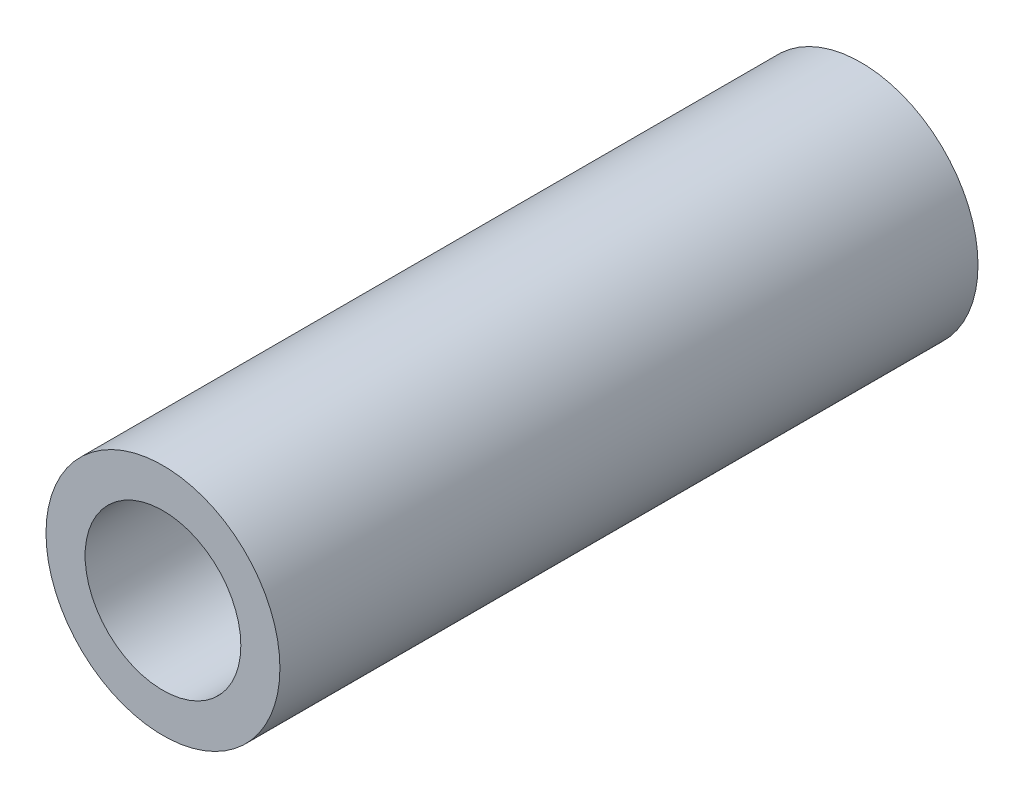
SolidWorks part; units mm, degrees
ref_plane "Front Plane" through (0, 0, 0) normal (0, 0, 1) x (1, 0, 0)
ref_plane "Top Plane" through (0, 0, 0) normal (0, 1, 0) x (1, 0, 0)
ref_plane "Right Plane" through (0, 0, 0) normal (1, 0, 0) x (0, 0, -1)
sketch "Sketch1" plane through (0, 0, 0) normal (0, 0, 1) x (1, 0, 0)
  circle A0 centre (0, 0) radius 4.7879
  circle A1 centre (0, 0) radius 3.1877
  dimension "OD" = 9.5758
  dimension "ID" = 6.3754
sketch "Sketch2" plane through (0, 0, 0) normal (1, 0, 0) x (0, 0, -1)
  line L2 (14.2875, 0) -> (-14.2875, 0) construction
  line L4 (-14.2875, -4.7879) -> (-14.2875, 4.7879) construction
  line L5 (-14.2875, -3.1877) -> (14.2875, -3.1877)
  line L6 (14.2875, 3.1877) -> (-14.2875, 3.1877)
  line L7 (14.2875, -4.7879) -> (14.2875, 4.7879) construction
  line L8 (-14.2875, 4.7879) -> (14.2875, 4.7879) construction
  line L9 (-14.2875, -4.7879) -> (14.2875, -4.7879) construction
  line L10 (0, 4.7879) -> (0, -4.7879) construction
  line L11 (0, 3.1877) -> (0, -3.1877) construction
  point P4 (0, -3.1877)
  point P7 (0, 3.1877)
  point P8 (0, 0)
  point P12 (-14.2875, 0)
  point P15 (14.2875, 0)
  point P16 (0, -4.7879)
  point P17 (0, 4.7879)
  dimension "Length" = 28.575
sketch "Sketch5" plane through (0, 0, 0) normal (0, 0, 1) x (1, 0, 0)
  circle A1 centre (0, 0) radius 3.1877
  circle A2 centre (0, 0) radius 3.1877
  circle A3 centre (0, 0) radius 4.7879
  circle A4 centre (0, 0) radius 4.7879
  dimension "D1" = 0
  dimension "D2" = 0
extrude "Boss-Extrude1" add sketch "Sketch5" along normal mid plane 28.575
equation "\"D1@Boss-Extrude1\" = \"Length@Sketch2\""
